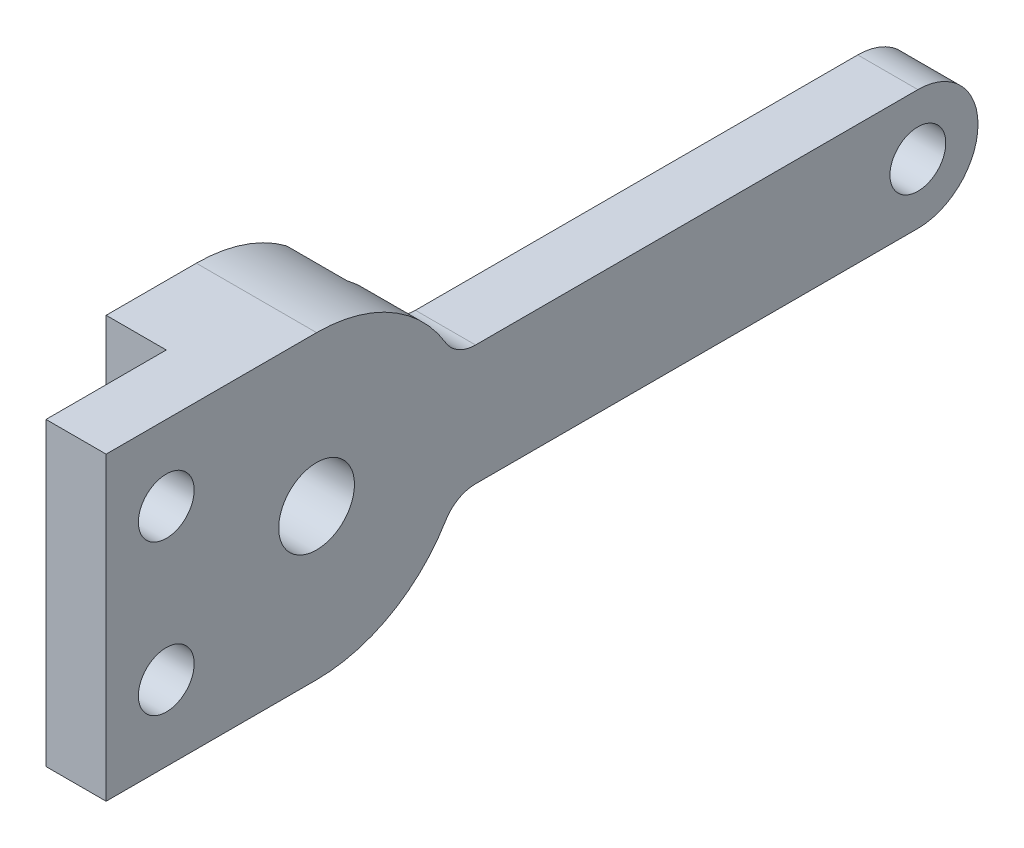
SolidWorks part; units mm, degrees
material "6061-T6 (SS)"
ref_plane "Front Plane" through (0, 0, 0) normal (0, 0, 1) x (1, 0, 0)
ref_plane "Top Plane" through (0, 0, 0) normal (0, 1, 0) x (1, 0, 0)
ref_plane "Right Plane" through (0, 0, 0) normal (1, 0, 0) x (0, 0, -1)
sketch "Sketch1" plane through (0, 0, 0) normal (1, 0, 0) x (0, 0, -1)
  line L0 (-4.7625, -1000.0694) -> (-4.7625, 48999.9306) construction
  line L1 (-11.1125, 7.9375) -> (0, 7.9375)
  line L2 (-11.1125, 7.9375) -> (-11.1125, -7.9375)
  line L3 (-11.1125, -7.9375) -> (0, -7.9375)
  line L4 (2.0986, 7.9375) -> (2.0986, -7.9375) construction
  line L5 (-11.1125, 7.9375) -> (2.0986, -7.9375) construction
  line L6 (-11.1125, -7.9375) -> (2.0986, 7.9375) construction
  line L8 (31.75, -3.175) -> (7.2748, -3.175)
  line L9 (34.925, -3.175) -> (34.925, 3.175) construction
  line L10 (31.75, 3.175) -> (7.2748, 3.175)
  line L12 (34.925, -3.175) -> (7.2748, 3.175) construction
  line L13 (34.925, 3.175) -> (7.2748, -3.175) construction
  circle A0 centre (0, 0) radius 2
  arc A1 (0, 7.9375) -> (7.2748, 3.175) centre (0, 0) cw
  arc A2 (7.2748, -3.175) -> (0, -7.9375) centre (0, 0) cw
  arc A5 (31.75, 3.175) -> (31.75, -3.175) centre (31.75, 0) cw
  point P3 (-4.5069, 0)
  point P12 (31.75, 3.175)
  point P13 (35.422, -3.175)
  point P18 (21.0999, 0)
  point P24 (18.188, 0)
  point P28 (17.1441, -0.6297)
  point P29 (0, 0)
  point P30 (21.7136, 0)
  dimension "D1" = 4
  dimension "D2" = 15.875
  dimension "D3" = 4.7625
  dimension "D4" = 6.35
  dimension "D5" = 6.35
  dimension "D6" = 31.75
extrude "Boss-Extrude1" add sketch "Sketch1" along normal blind 6.35
fillet "Fillet1" radius 1.8415 2 edges at (3.175, -3.175, -7.2748) (3.175, 3.175, -7.2748)
sketch "Sketch2" plane through (0, 0, 0) normal (-1, 0, 0) x (0, 0, 1)
  line L0 (11.1125, -7.9375) -> (0, -7.9375) construction
  line L1 (11.1125, 7.9375) -> (4.7625, 7.9375)
  line L2 (11.1125, 7.9375) -> (11.1125, -7.9375)
  line L3 (11.1125, -7.9375) -> (4.7625, -7.9375)
  line L4 (4.7625, 7.9375) -> (4.7625, -7.9375)
  line L5 (-4.7625, 0.6977) -> (4.7625, -0.6977) construction
  line L6 (-47.1497, 11.8611) -> (-4.7625, 11.8611)
  line L7 (-47.1497, 11.8611) -> (-47.1497, -14.4025)
  line L8 (-47.1497, -14.4025) -> (-4.7625, -14.4025)
  line L9 (-4.7625, 11.8611) -> (-4.7625, -14.4025)
  dimension "D1" = 6.35
extrude "Cut-Extrude1" cut sketch "Sketch2" against normal blind 3.175
hole_wizard "#4 Clearance Hole1" positions "Sketch3" profile "Sketch4" hole size "#4" standard "ANSI Inch" end condition through all
sketch "Sketch3" plane through (6.35, 0, 0) normal (1, 0, 0) x (0, 0, -1)
  line L0 (-7.9375, -3.9688) -> (0, 0)
  line L1 (0, 0) -> (-7.9375, 3.9688)
  line L3 (-11.1125, 7.9375) -> (-11.1125, -7.9375) construction
  point P0 (-7.9375, 3.9688)
  point P2 (-7.9375, -3.9688)
  point P12 (0, 0)
  point P17 (-10.2195, -6.1236)
  point P18 (0, 0)
  dimension "D1" = 7.9375
  dimension "D2" = 3.175
sketch "Sketch4" plane through (6.35, 3.9688, 7.9375) normal (0, 1, 0) x (0, 0, -1)
  line L0 (0, 0) -> (0, 6.35)
  line L1 (0, 6.35) -> (1.4732, 6.35)
  line L2 (1.4732, 6.35) -> (1.4732, 0)
  line L5 (1.4732, 0) -> (0, 0)
  line L11 (0, -6.35) -> (0, 107.95) construction
  dimension "Thru Hole Dia." = 2.9464
  dimension "Thru Hole Depth" = 6.35
hole_wizard "#4 Clearance Hole2" positions "Sketch5" profile "Sketch6" hole size "#4" standard "ANSI Inch" end condition through all
sketch "Sketch5" plane through (3.175, 0, 0) normal (-1, 0, 0) x (0, 0, 1)
  arc A0 (-31.75, 3.175) -> (-31.75, -3.175) centre (-31.75, 0) ccw construction
  point P0 (-31.75, 0)
sketch "Sketch6" plane through (3.175, 0, -31.75) normal (0, 1, 0) x (0, 0, 1)
  line L0 (0, 0) -> (0, 3.175)
  line L1 (0, 3.175) -> (1.4732, 3.175)
  line L2 (1.4732, 3.175) -> (1.4732, 0)
  line L5 (1.4732, 0) -> (0, 0)
  line L11 (0, -6.35) -> (0, 107.95) construction
  dimension "Thru Hole Dia." = 2.9464
  dimension "Thru Hole Depth" = 3.175
